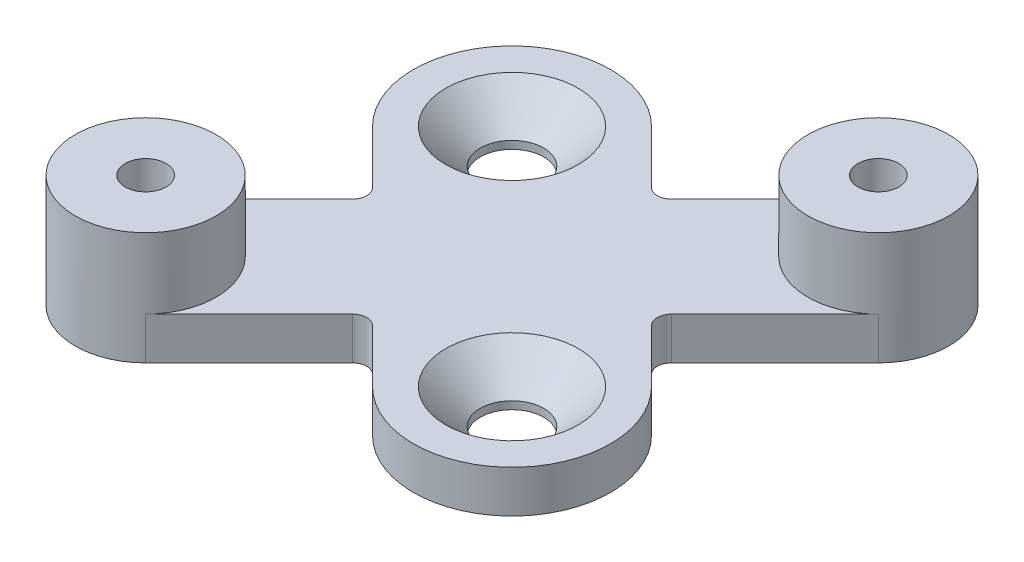
SolidWorks part; units mm, degrees
ref_plane "Front Plane" through (0, 0, 0) normal (0, 0, 1) x (1, 0, 0)
ref_plane "Top Plane" through (0, 0, 0) normal (0, 1, 0) x (1, 0, 0)
ref_plane "Right Plane" through (0, 0, 0) normal (1, 0, 0) x (0, 0, -1)
sketch "Sketch1" plane through (0, 0, 0) normal (0, 1, 0) x (1, 0, 0)
  line L0 (97.3748, 97.3748) -> (35423.8599, 35423.8599) construction
  line L1 (0, 0) -> (0, 50000) construction
  line L2 (-0.3108, 0.3108) -> (-35326.7959, 35326.7959) construction
  line L3 (-16.5355, -9.4645) -> (-8.4853, -1.4142)
  line L4 (16.5355, 9.4645) -> (8.4853, 1.4142)
  line L5 (3.0503, -12.9497) -> (-1.4142, -8.4853)
  line L6 (-3.0503, 12.9497) -> (1.4142, 8.4853)
  line L7 (-8.4853, -1.4142) -> (-12.9497, 3.0503)
  line L8 (1.4142, 8.4853) -> (9.4645, 16.5355)
  line L9 (-1.4142, -8.4853) -> (-9.4645, -16.5355)
  line L10 (8.4853, 1.4142) -> (12.9497, -3.0503)
  arc A0 (-16.5355, -9.4645) -> (-9.4645, -16.5355) centre (-13, -13) ccw
  arc A1 (16.5355, 9.4645) -> (9.4645, 16.5355) centre (13, 13) ccw
  arc A2 (-3.0503, 12.9497) -> (-12.9497, 3.0503) centre (-8, 8) ccw
  arc A3 (3.0503, -12.9497) -> (12.9497, -3.0503) centre (8, -8) ccw
  dimension "D2" = 5
  dimension "D4" = 7
  dimension "D1" = 45
  dimension "D3" = 26
  dimension "D5" = 16
extrude "Boss-Extrude1" add sketch "Sketch1" along normal blind 3
fillet "Fillet1" radius 1 4 edges at (-8.4853, 1.5, 1.4142) (1.4142, 1.5, -8.4853) (8.4853, 1.5, -1.4142) (-1.4142, 1.5, 8.4853)
hole_wizard "CSK for M4 Countersunk Flat Head Screw1" positions "Sketch3" profile "Sketch2" countersink size "M4" standard "ISO" end condition through all
sketch "Sketch3" plane through (0, 3, 0) normal (0, 1, 0) x (1, 0, 0)
  arc A0 (-3.0503, 12.9497) -> (-12.9497, 3.0503) centre (-8, 8) ccw construction
  arc A1 (3.0503, -12.9497) -> (12.9497, -3.0503) centre (8, -8) ccw construction
  point P0 (-8, 8)
  point P2 (8, -8)
sketch "Sketch2" plane through (-8, 3, -8) normal (1, 0, 0) x (0, 0, 1)
  line L0 (0, 0) -> (0, 3)
  line L1 (0, 3) -> (2.25, 3)
  line L2 (2.25, 3) -> (2.25, 2.45)
  line L3 (2.25, 2.45) -> (4.7, 0)
  line L5 (4.7, 0) -> (0, 0)
  line L6 (-2.25, 2.45) -> (-4.7, 0) construction
  line L11 (0, -6.35) -> (0, 107.95) construction
  dimension "Thru Hole Dia." = 4.5
  dimension "Thru Hole Depth" = 3
  dimension "Near C'Sink Dia." = 9.4
  dimension "Near C'Sink Angle" = 90
sketch "Sketch4" plane through (0, 3, 0) normal (0, 1, 0) x (1, 0, 0)
  circle A0 centre (-13, -13) radius 5
  circle A1 centre (13, 13) radius 5
  arc A2 (16.5355, 9.4645) -> (9.4645, 16.5355) centre (13, 13) ccw construction
  arc A3 (-16.5355, -9.4645) -> (-9.4645, -16.5355) centre (-13, -13) ccw construction
extrude "Boss-Extrude2" add sketch "Sketch4" along normal blind 5
sketch "Sketch5" plane through (0, 8, 0) normal (0, 1, 0) x (1, 0, 0)
  circle A0 centre (-13, -13) radius 1.45
  circle A1 centre (13, 13) radius 1.45
  dimension "D1" = 2.9
extrude "Cut-Extrude1" cut sketch "Sketch5" against normal through all
